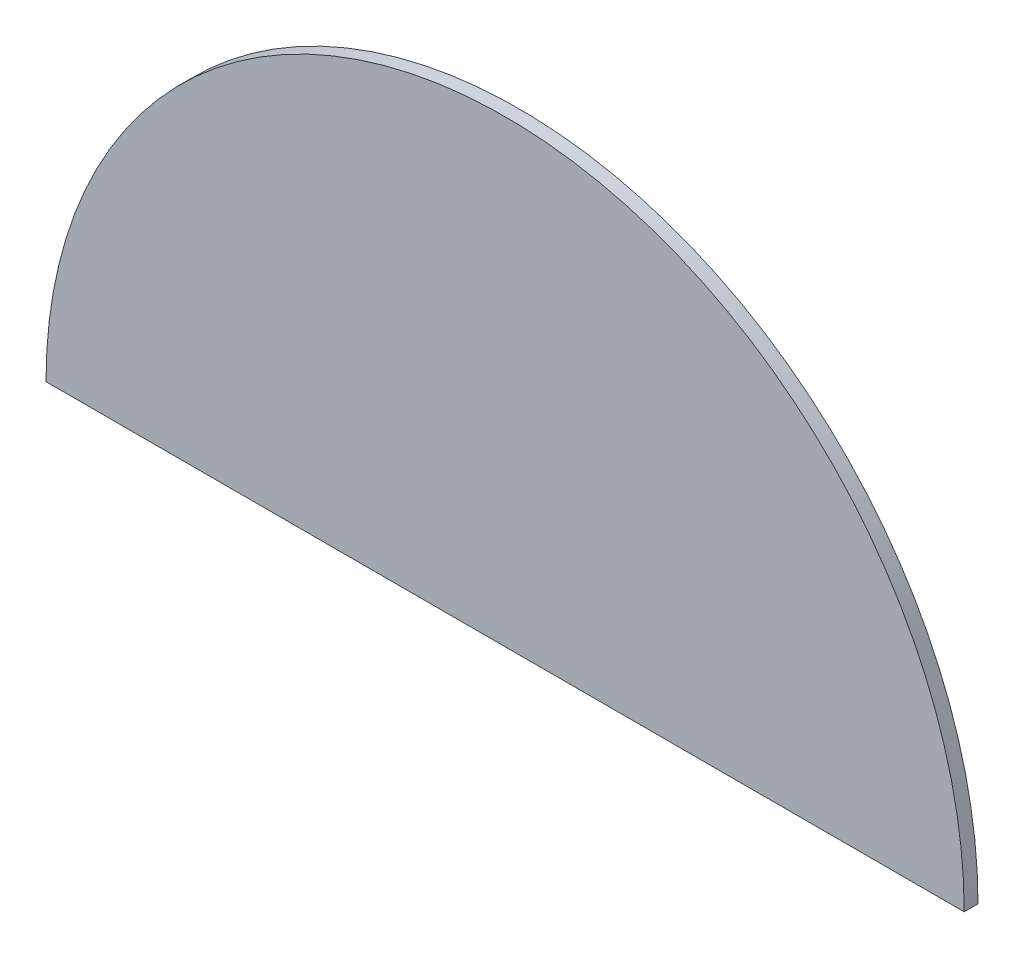
SolidWorks part; units mm, degrees
ref_plane "Plan de face" through (0, 0, 0) normal (0, 0, 1) x (1, 0, 0)
ref_plane "Plan de dessus" through (0, 0, 0) normal (0, 1, 0) x (1, 0, 0)
ref_plane "Plan de droite" through (0, 0, 0) normal (1, 0, 0) x (0, 0, -1)
sketch "Esquisse1" plane through (0, 0, 0) normal (0, 0, 1) x (1, 0, 0)
  line L0 (-100, 0) -> (100, 0)
  arc A0 (-100, 0) -> (100, 0) centre (0, 0) cw
  dimension "D1" = 100
extrude "Boss.-Extru.1" add sketch "Esquisse1" along normal blind 3
